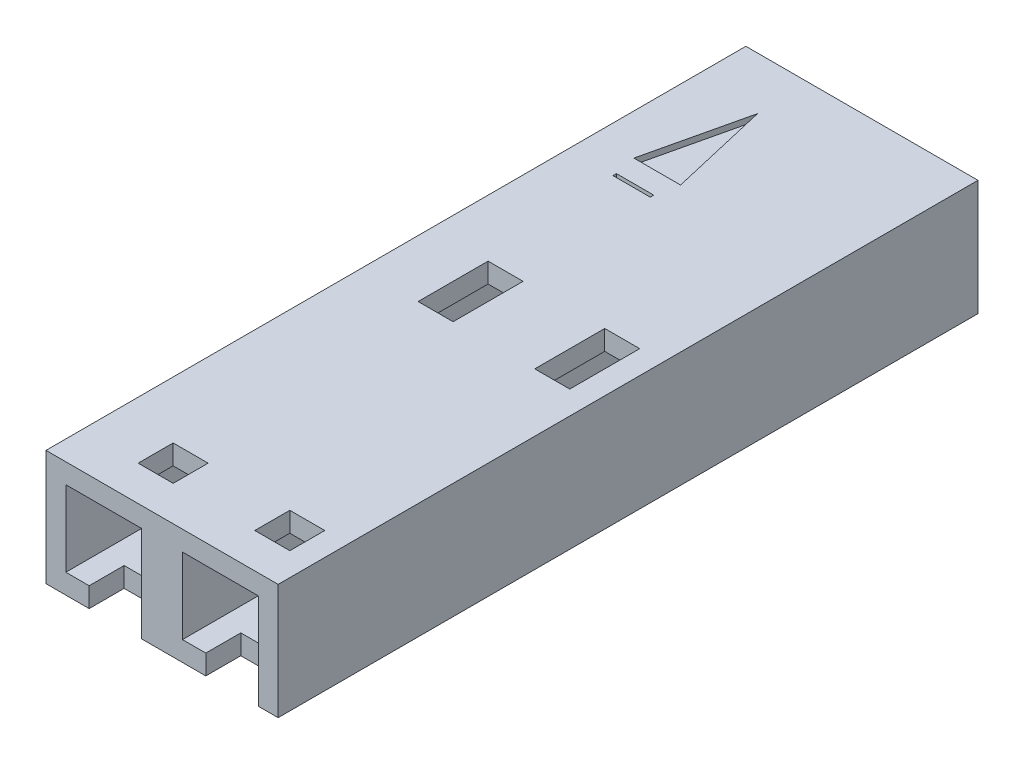
SolidWorks part; units mm, degrees
ref_plane "Front" through (0, 0, 0) normal (0, 0, 1) x (1, 0, 0)
ref_plane "Top" through (0, 0, 0) normal (0, 1, 0) x (1, 0, 0)
ref_plane "Right" through (0, 0, 0) normal (1, 0, 0) x (0, 0, -1)
sketch "Sketch1" plane through (0, 0, 0) normal (0, 0, 1) x (1, 0, 0)
  line L0 (0, 0) -> (5.0546, 0)
  line L1 (5.0546, 0) -> (5.0546, 2.5146)
  line L2 (5.0546, 2.5146) -> (0, 2.5146)
  line L3 (0, 2.5146) -> (0, 0)
  dimension "D1" = 5.0546
  dimension "D2" = 2.5146
extrude "Boss-Extrude1" add sketch "Sketch1" along normal blind 15.24
sketch "Sketch2" plane through (0, 0, 0) normal (0, 0, -1) x (-1, 0, 0)
  line L0 (-4.3688, 1.8288) -> (-3.2258, 1.8288)
  line L1 (-3.2258, 1.8288) -> (-3.2258, 0.6858)
  line L2 (-3.2258, 0.6858) -> (-4.3688, 0.6858)
  line L3 (-4.3688, 0.6858) -> (-4.3688, 1.8288)
  line L4 (-1.8288, 1.8288) -> (-0.6858, 1.8288)
  line L5 (-0.6858, 1.8288) -> (-0.6858, 0.6858)
  line L6 (-0.6858, 0.6858) -> (-1.8288, 0.6858)
  line L7 (-1.8288, 0.6858) -> (-1.8288, 1.8288)
  line L8 (-3.7973, 1.8288) -> (-3.7973, 0.6858) construction
  line L9 (-1.2573, 1.8288) -> (-1.2573, 0.6858) construction
  line L10 (-3.2258, 1.2573) -> (-4.3688, 1.2573) construction
  line L11 (-0.6858, 1.2573) -> (-1.8288, 1.2573) construction
  line L12 (-2.5273, 2.5146) -> (-2.5273, 0) construction
  line L13 (-5.0546, 2.5146) -> (0, 2.5146) construction
  line L14 (0, 0) -> (-5.0546, 0) construction
  dimension "D1" = 2.54
  dimension "D2" = 1.143
  dimension "D3" = 1.143
  dimension "D4" = 1.143
  dimension "D5" = 1.143
  dimension "D6" = 1.2573
  dimension "D7" = 1.2573
extrude "Cut-Extrude1" cut sketch "Sketch2" against normal through all
chamfer "Chamfer1" distance 0.254 angle 45 8 edges at (0.6858, 1.2573, 0) (1.2573, 0.6858, 0) (1.8288, 1.2573, 0) (1.2573, 1.8288, 0) (4.3688, 1.2573, 0) (3.7973, 0.6858, 0) (3.2258, 1.2573, 0) (3.7973, 1.8288, 0)
sketch "Sketch3" plane through (0, 2.5146, 0) normal (0, 1, 0) x (1, 0, 0)
  line L0 (3.7846, -13.716) -> (4.5466, -13.716)
  line L1 (4.5466, -13.716) -> (4.5466, -14.478)
  line L2 (4.5466, -14.478) -> (3.7846, -14.478)
  line L3 (3.7846, -14.478) -> (3.7846, -13.716)
  line L4 (1.2446, -13.716) -> (2.0066, -13.716)
  line L5 (2.0066, -13.716) -> (2.0066, -14.478)
  line L6 (2.0066, -14.478) -> (1.2446, -14.478)
  line L7 (1.2446, -14.478) -> (1.2446, -13.716)
  line L8 (1.6256, -13.716) -> (1.6256, -14.478) construction
  line L9 (4.1656, -13.716) -> (4.1656, -14.478) construction
  line L10 (1.2446, -14.097) -> (2.0066, -14.097) construction
  line L11 (3.7846, -14.097) -> (4.5466, -14.097) construction
  line L12 (5.0546, -15.24) -> (0, -15.24) construction
  line L13 (5.0546, -15.24) -> (5.0546, 0) construction
  line L14 (3.7846, -8.382) -> (3.7846, -6.858)
  line L15 (3.7846, -6.858) -> (4.5466, -6.858)
  line L16 (4.5466, -6.858) -> (4.5466, -8.382)
  line L17 (4.5466, -8.382) -> (3.7846, -8.382)
  line L18 (1.2446, -6.858) -> (2.0066, -6.858)
  line L19 (2.0066, -6.858) -> (2.0066, -8.382)
  line L20 (2.0066, -8.382) -> (1.2446, -8.382)
  line L21 (1.2446, -8.382) -> (1.2446, -6.858)
  line L22 (0, -7.62) -> (5.0546, -7.62) construction
  line L23 (0, -15.24) -> (0, 0) construction
  line L24 (1.2446, -7.62) -> (2.0066, -7.62) construction
  line L25 (3.7846, -7.62) -> (4.5466, -7.62) construction
  dimension "D1" = 0.381
  dimension "D2" = 0.381
  dimension "D3" = 0.381
  dimension "D4" = 0.381
  dimension "D5" = 2.54
  dimension "D6" = 0.762
  dimension "D7" = 0.508
  dimension "D8" = 1.524
extrude "Cut-Extrude2" cut sketch "Sketch3" against normal blind 1.27
ref_plane "Plane1" through (0, 0, 0.508) normal (0, 0, 1) x (1, 0, 0)
sketch "Sketch4" plane through (0, 0, 0.508) normal (0, 0, 1) x (1, 0, 0)
  line L0 (2.0828, 2.0828) -> (0.4318, 2.0828) construction
  line L1 (0.4318, 2.0828) -> (0.4318, 0.4318) construction
  line L2 (0.4318, 0.4318) -> (2.0828, 0.4318) construction
  line L3 (2.0828, 0.4318) -> (2.0828, 2.0828) construction
  line L4 (2.9718, 2.0828) -> (2.9718, 0.4318) construction
  line L5 (4.6228, 2.0828) -> (2.9718, 2.0828) construction
  line L6 (4.6228, 0.4318) -> (4.6228, 2.0828) construction
  line L7 (2.9718, 0.4318) -> (4.6228, 0.4318) construction
  line L8 (2.0828, 2.0828) -> (0.4318, 2.0828)
  line L9 (0.4318, 2.0828) -> (0.4318, 0.4318)
  line L10 (0.4318, 0.4318) -> (2.0828, 0.4318)
  line L11 (2.0828, 0.4318) -> (2.0828, 2.0828)
  line L12 (2.9718, 2.0828) -> (2.9718, 0.4318)
  line L13 (4.6228, 2.0828) -> (2.9718, 2.0828)
  line L14 (4.6228, 0.4318) -> (4.6228, 2.0828)
  line L15 (2.9718, 0.4318) -> (4.6228, 0.4318)
extrude "Cut-Extrude3" cut sketch "Sketch4" along normal through all
sketch "Sketch6" plane through (0, 0, 0) normal (0, -1, 0) x (1, 0, 0)
  line L0 (0.9398, 15.24) -> (2.0828, 15.24)
  line L1 (0, 15.24) -> (5.0546, 15.24) construction
  line L2 (2.0828, 15.24) -> (2.0828, 14.478)
  line L3 (2.0828, 15.24) -> (2.0828, 0.508) construction
  line L4 (2.0828, 14.478) -> (0.9398, 14.478)
  line L5 (0.9398, 14.478) -> (0.9398, 15.24)
  line L6 (4.6228, 15.24) -> (4.6228, 14.478)
  line L7 (4.6228, 15.24) -> (4.6228, 0.508) construction
  line L8 (4.6228, 14.478) -> (3.4798, 14.478)
  line L9 (3.4798, 14.478) -> (3.4798, 15.24)
  line L10 (3.4798, 15.24) -> (4.6228, 15.24)
  line L11 (1.2446, 14.478) -> (2.0066, 14.478) construction
  dimension "D1" = 1.143
  dimension "D2" = 1.143
extrude "Cut-Extrude5" cut sketch "Sketch6" against normal up to surface (0.4318 mm away) up to face at (1.2573, 0.4318, 7.874)
sketch "Sketch7" plane through (0, 0, 0) normal (0, -1, 0) x (1, 0, 0)
  line L0 (2.2098, 7.62) -> (2.7178, 7.62)
  line L1 (2.7178, 7.62) -> (2.7178, 0)
  line L2 (0, 0) -> (5.0546, 0) construction
  line L3 (2.7178, 0) -> (2.2098, 0)
  line L4 (2.2098, 0) -> (2.2098, 7.62)
  line L5 (5.0546, 7.62) -> (0, 7.62) construction
  line L6 (5.0546, 15.24) -> (5.0546, 0) construction
  line L7 (0, 15.24) -> (0, 0) construction
  line L8 (2.0828, 14.478) -> (2.0828, 0.508) construction
  dimension "D1" = 0.127
  dimension "D2" = 0.508
extrude "Cut-Extrude6" cut sketch "Sketch7" against normal blind 0.762
sketch "Sketch8" plane through (0, 2.5146, 0) normal (0, 1, 0) x (1, 0, 0)
  line L0 (1.397, -1.143) -> (0.889, -3.3274)
  line L1 (0.889, -3.3274) -> (1.905, -3.3274)
  line L2 (1.905, -3.3274) -> (1.397, -1.143)
  line L3 (1.397, 1.3415) -> (1.397, -3.8862) construction
  line L4 (0.9906, -3.81) -> (1.8034, -3.81)
  line L5 (1.8034, -3.81) -> (1.8034, -3.8862)
  line L6 (1.8034, -3.8862) -> (0.9906, -3.8862)
  line L7 (0.9906, -3.81) -> (0.9906, -3.8862)
  line L8 (5.0546, 0) -> (0, 0) construction
  dimension "D1" = 2.1844
  dimension "D2" = 1.016
  dimension "D3" = 0.8128
  dimension "D4" = 0.0762
  dimension "D5" = 1.143
  dimension "D6" = 2.667
  dimension "D7" = 1.397
extrude "Cut-Extrude7" cut sketch "Sketch8" against normal blind 0.127
